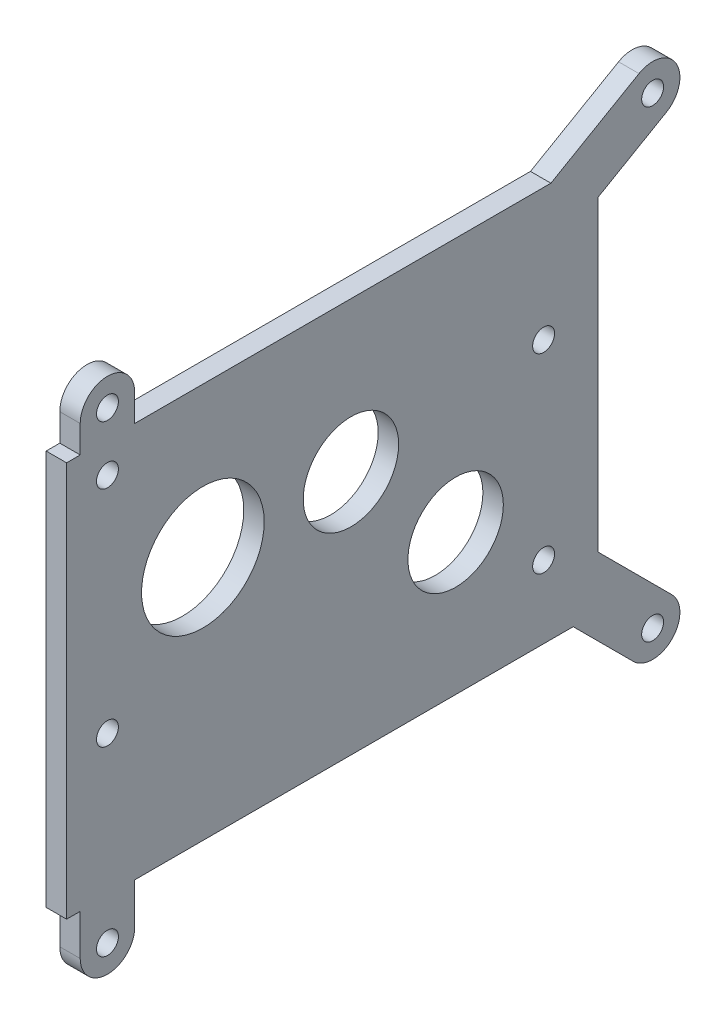
SolidWorks part; units mm, degrees
material "5052-H32"
ref_plane "Front Plane" through (0, 0, 0) normal (0, 0, 1) x (1, 0, 0)
ref_plane "Top Plane" through (0, 0, 0) normal (0, 1, 0) x (1, 0, 0)
ref_plane "Right Plane" through (0, 0, 0) normal (1, 0, 0) x (0, 0, -1)
sketch "Sketch1" plane through (0, 0, 0) normal (1, 0, 0) x (0, 0, -1)
  line L1 (0, 0) -> (123.825, 0)
  line L2 (0, 0) -> (0, 92.075)
  line L3 (0, 92.075) -> (123.825, 92.075)
  line L4 (123.825, 0) -> (123.825, 92.075)
  dimension "D1" = 123.825
  dimension "D2" = 92.075
extrude "Boss-Extrude2" add sketch "Sketch1" along normal blind 4.7625
sketch "Sketch2" plane through (4.7625, 0, 0) normal (1, 0, 0) x (0, 0, -1)
  circle A1 centre (66.2432, 57.15) radius 11.1125
  circle A7 centre (66.2432, 57.15) radius 11.1125
  circle A8 centre (31.75, 57.15) radius 11.1125
  circle A9 centre (31.75, 57.15) radius 11.1125
  circle A10 centre (90.6336, 32.7596) radius 14.2875
  circle A11 centre (90.6336, 32.7596) radius 14.2875
  dimension "D1" = 0
  dimension "D2" = 0
  dimension "D3" = 0
extrude "Cut-Extrude1" cut sketch "Sketch2" against normal through all
hole_wizard "#10 Clearance Hole1" positions "Sketch5" profile "Sketch6" hole size "#10" standard "ANSI Inch" end condition through all
sketch "Sketch5" plane through (4.7625, 0, 0) normal (1, 0, 0) x (0, 0, -1)
  circle A1 centre (111.125, 61.3346) radius 2.5527 construction
  circle A2 centre (9.525, 84.8296) radius 2.5527 construction
  circle A3 centre (9.525, 32.7596) radius 2.5527 construction
  circle A5 centre (111.125, 61.3346) radius 2.5527
  circle A6 centre (9.525, 84.8296) radius 2.5527
  circle A7 centre (9.525, 32.7596) radius 2.5527
  circle A8 centre (111.125, 16.8846) radius 2.5527 construction
  circle A9 centre (111.125, 16.8846) radius 2.5527
  point P423 (9.525, 84.8296)
  point P426 (111.125, 61.3346)
  point P432 (9.525, 32.7596)
  point P469 (111.125, 16.8846)
sketch "Sketch6" plane through (4.7625, 84.8296, -9.525) normal (0, 1, 0) x (0, 0, -1)
  line L0 (0, 0) -> (0, 4.7625)
  line L1 (0, 4.7625) -> (2.5527, 4.7625)
  line L2 (2.5527, 4.7625) -> (2.5527, 0)
  line L5 (2.5527, 0) -> (0, 0)
  line L11 (0, -6.35) -> (0, 107.95) construction
  dimension "Thru Hole Dia." = 5.1054
  dimension "Thru Hole Depth" = 4.7625
sketch "Sketch7" plane through (4.7625, 0, 0) normal (1, 0, 0) x (0, 0, -1)
  line L0 (9.525, 32.7596) -> (31.75, 57.15) construction
  line L1 (31.75, 57.15) -> (9.525, 84.8296) construction
  line L2 (31.75, 57.15) -> (66.2432, 57.15) construction
  line L3 (66.2432, 57.15) -> (90.6336, 32.7596) construction
  line L4 (90.6336, 32.7596) -> (111.125, 16.8846) construction
  line L5 (90.6336, 32.7596) -> (111.125, 61.3346) construction
  line L6 (111.125, 61.3346) -> (66.2432, 57.15) construction
  line L7 (93.3939, 66.059) -> (103.4666, 66.9981)
  line L8 (108.2058, 46.3673) -> (112.148, 51.8647)
  line L9 (19.0004, 33.7303) -> (17.6786, 32.2798)
  line L10 (8.2914, 40.8337) -> (9.6131, 42.2842)
  line L12 (0, 92.075) -> (123.825, 92.075)
  line L13 (0, 92.075) -> (0, 0)
  line L14 (0, 0) -> (123.825, 0)
  line L15 (123.825, 92.075) -> (123.825, 0)
  circle A0 centre (31.75, 57.15) radius 28.575 construction
  circle A1 centre (66.2432, 57.15) radius 28.575 construction
  circle A2 centre (90.6336, 32.7596) radius 22.225 construction
  circle A3 centre (111.125, 16.8846) radius 9.525 construction
  circle A4 centre (111.125, 61.3346) radius 9.525 construction
  circle A5 centre (9.525, 32.7596) radius 9.525 construction
  circle A6 centre (9.525, 84.8296) radius 9.525 construction
  arc A7 (103.4666, 66.9981) -> (112.148, 51.8647) centre (111.125, 61.3346) cw
  arc A8 (108.2058, 46.3673) -> (111.9221, 26.3762) centre (90.6336, 32.7596) cw
  arc A9 (111.9221, 26.3762) -> (102.1336, 13.7412) centre (111.125, 16.8846) cw
  arc A10 (102.1336, 13.7412) -> (68.7847, 28.6882) centre (90.6336, 32.7596) cw
  arc A11 (68.7847, 28.6882) -> (48.9966, 34.3666) centre (66.2432, 57.15) cw
  arc A12 (48.9966, 34.3666) -> (17.6786, 32.2798) centre (31.75, 57.15) cw
  arc A13 (19.0004, 33.7303) -> (9.6131, 42.2842) centre (9.525, 32.7596) cw
  arc A14 (8.2914, 40.8337) -> (9.6844, 75.306) centre (31.75, 57.15) cw
  arc A15 (9.6844, 75.306) -> (18.7894, 82.6167) centre (9.525, 84.8296) cw
  arc A16 (18.7894, 82.6167) -> (48.9966, 79.9334) centre (31.75, 57.15) cw
  arc A17 (48.9966, 79.9334) -> (93.3939, 66.059) centre (66.2432, 57.15) cw
  line M17 (0, 92.075) -> (0, 0)
  line M18 (0, 0) -> (123.825, 0)
  line M19 (123.825, 0) -> (123.825, 92.075)
  line M20 (123.825, 92.075) -> (0, 92.075)
  dimension "D1" = 19.05
  dimension "D2" = 19.05
  dimension "D3" = 57.15
  dimension "D4" = 57.15
  dimension "D5" = 44.45
  dimension "D6" = 19.05
  dimension "D7" = 19.05
  dimension "D8" = 6.35
  dimension "D9" = 6.35
  dimension "D10" = 6.35
  dimension "D11" = 6.35
extrude "Cut-Extrude2" [suppressed] cut sketch "Sketch7" against normal through all contours A16 A17 L7 A7 L8 A8 A9 A10 A11 A12 L9 A13 L13 A15 M18 M19 M20 M17 | A14 A15 L13 A13 L10
fillet "Fillet1" [suppressed] radius 4.7625
sketch "Sketch8" plane through (4.7625, 0, 0) normal (1, 0, 0) x (0, 0, -1)
  circle A0 centre (31.75, 57.15) radius 14.2875
  circle A1 centre (31.75, 57.15) radius 11.1125 construction
  circle A2 centre (31.75, 57.15) radius 11.1125
  dimension "D1" = 28.575
sketch "Sketch9" plane through (4.7625, 0, 0) normal (1, 0, 0) x (0, 0, -1)
  circle A0 centre (90.6336, 32.7596) radius 11.1125
  circle A1 centre (90.6336, 32.7596) radius 14.2875 construction
  circle A2 centre (90.6336, 32.7596) radius 14.2875
  dimension "D1" = 22.225
extrude "Cut-Extrude3" cut sketch "Sketch8" against normal through all contours A0
extrude "Boss-Extrude3" add sketch "Sketch9" against normal up to surface (4.7625 mm away) contours A0
sketch "Sketch10" plane through (0, 0, 0) normal (-1, 0, 0) x (0, 0, 1)
  line L1 (-136.525, -9.525) -> (-9.525, -9.525) construction
  line L2 (-136.525, -9.525) -> (-136.525, 98.425) construction
  line L3 (-136.525, 98.425) -> (-9.525, 98.425) construction
  line L4 (-9.525, -9.525) -> (-9.525, 98.425) construction
  circle A4 centre (-31.75, 57.15) radius 14.2875 construction
  dimension "D1" = 66.675
  dimension "D2" = 22.225
  dimension "D3" = 127
  dimension "D4" = 107.95
sketch "Sketch11" plane through (0, 0, 0) normal (-1, 0, 0) x (0, 0, 1)
  line L0 (-132.0349, -14.0151) -> (-118.0197, 0)
  line L1 (0, 0) -> (-123.825, 0) construction
  line L2 (-141.0151, -5.0349) -> (-123.825, 12.1553)
  line L3 (-123.825, 0) -> (-123.825, 92.075) construction
  line L4 (-139.7, 92.9257) -> (-123.825, 83.7603)
  line L5 (-15.875, -9.525) -> (-15.875, 0)
  line L6 (-133.35, 103.9243) -> (-112.8265, 92.075)
  line L7 (-123.825, 92.075) -> (0, 92.075) construction
  line L8 (-3.175, -9.525) -> (-3.175, 0)
  line L9 (-3.175, 0) -> (-15.875, 0)
  line L10 (-15.875, 98.425) -> (-15.875, 92.075)
  line L11 (-15.875, 92.075) -> (-3.175, 92.075)
  line L12 (-3.175, 92.075) -> (-3.175, 98.425)
  line L13 (-123.825, 83.7603) -> (-123.825, 92.075)
  line L14 (-123.825, 92.075) -> (-112.8265, 92.075)
  line L15 (-123.825, 12.1553) -> (-123.825, 0)
  line L16 (-123.825, 0) -> (-118.0197, 0)
  arc A0 (-141.0151, -5.0349) -> (-132.0349, -14.0151) centre (-136.525, -9.525) ccw
  arc A1 (-133.35, 103.9243) -> (-139.7, 92.9257) centre (-136.525, 98.425) ccw
  arc A2 (-3.175, 98.425) -> (-15.875, 98.425) centre (-9.525, 98.425) ccw
  arc A3 (-15.875, -9.525) -> (-3.175, -9.525) centre (-9.525, -9.525) ccw
  dimension "D1" = 12.7
  dimension "D2" = 135
  dimension "D3" = 120
extrude "Boss-Extrude4" add sketch "Sketch11" against normal up to surface (4.7625 mm away) up to face at (4.7625, 57.15, -46.0375)
hole_wizard "#10 Clearance Hole2" positions "Sketch13" profile "Sketch14" hole size "#10" standard "ANSI Inch" end condition through all
sketch "Sketch13" plane through (0, 0, 0) normal (-1, 0, 0) x (0, 0, 1)
  point P0 (-136.525, -9.525)
  point P3 (-136.525, 98.425)
  point P6 (-9.525, 98.425)
  point P9 (-9.525, -9.525)
sketch "Sketch14" plane through (0, -9.525, -136.525) normal (0, 1, 0) x (0, 0, 1)
  line L0 (0, 0) -> (0, 4.7625)
  line L1 (0, 4.7625) -> (2.5527, 4.7625)
  line L2 (2.5527, 4.7625) -> (2.5527, 0)
  line L5 (2.5527, 0) -> (0, 0)
  line L11 (0, -6.35) -> (0, 107.95) construction
  dimension "Thru Hole Dia." = 5.1054
  dimension "Thru Hole Depth" = 4.7625
